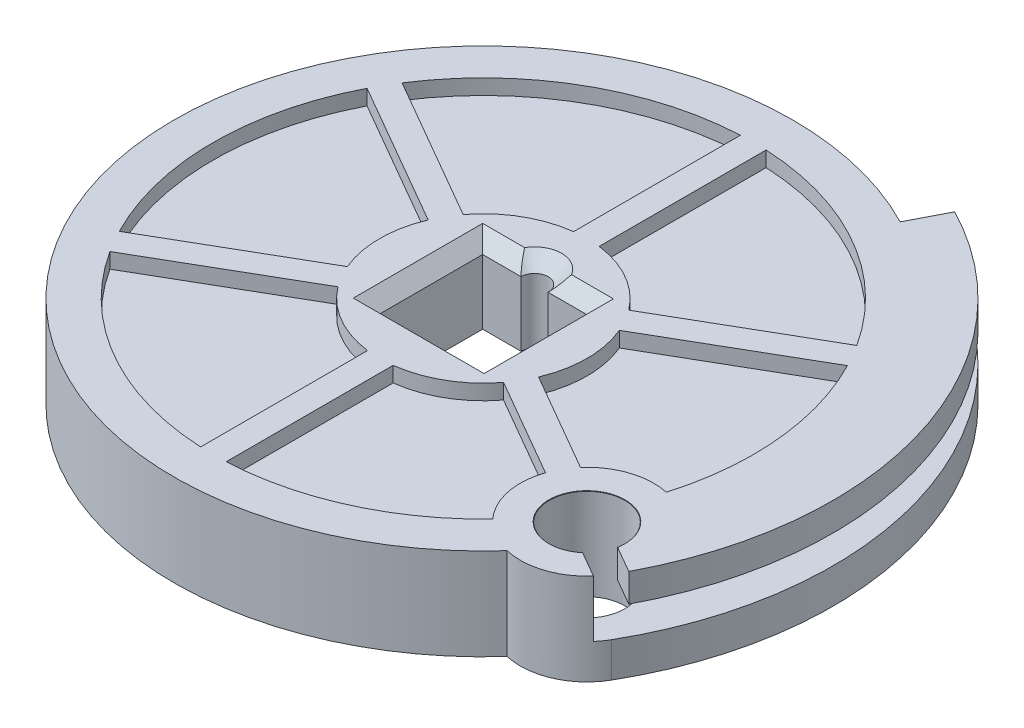
SolidWorks part; units mm, degrees
ref_plane "Plano frontal" through (0, 0, 0) normal (0, 0, 1) x (1, 0, 0)
ref_plane "Plano superior" through (0, 0, 0) normal (0, 1, 0) x (1, 0, 0)
ref_plane "Plano direito" through (0, 0, 0) normal (1, 0, 0) x (0, 0, -1)
sketch "Esboço1" plane through (0, 0, 0) normal (0, 1, 0) x (1, 0, 0)
  line L0 (0, 0) -> (0, 7.7) construction
  line L1 (0, 0) -> (6.6684, 3.85) construction
  line L2 (0, 0) -> (6.6684, -3.85) construction
  line L3 (0, 0) -> (0, -7.7) construction
  line L4 (0, 0) -> (-6.6684, -3.85) construction
  line L5 (0, 0) -> (-6.6684, 3.85) construction
  line L6 (0.95, 0) -> (0.95, 7.6412) construction
  line L7 (-0.95, 0) -> (-0.95, 7.6412) construction
  line L8 (0.475, -0.8227) -> (7.0924, 2.9979) construction
  line L9 (-0.475, 0.8227) -> (6.1424, 4.6433) construction
  line L10 (-0.475, -0.8227) -> (6.1424, -4.6433) construction
  line L11 (0.475, 0.8227) -> (7.0924, -2.9979) construction
  line L12 (-0.95, 0) -> (-0.95, -7.6412) construction
  line L13 (0.95, 0) -> (0.95, -7.6412) construction
  line L14 (-0.475, 0.8227) -> (-7.0924, -2.9979) construction
  line L15 (0.475, -0.8227) -> (-6.1424, -4.6433) construction
  line L16 (0.475, 0.8227) -> (-6.1424, 4.6433) construction
  line L17 (-0.475, -0.8227) -> (-7.0924, 2.9979) construction
  line L18 (-7.0924, 2.9979) -> (-17.8193, 9.191)
  line L19 (-17.8193, 9.191) -> (-20.3503, 10.6523) construction
  line L20 (-0.475, -0.8227) -> (-20.3503, 10.6523) construction
  line L21 (-6.6684, 3.85) -> (-17.3638, 10.025) construction
  line L22 (-17.3638, 10.025) -> (-19.8753, 11.475) construction
  line L23 (0, 0) -> (-19.8753, 11.475) construction
  line L24 (-6.1424, 4.6433) -> (-16.8693, 10.8365)
  line L25 (-16.8693, 10.8365) -> (-19.4003, 12.2977) construction
  line L26 (0.475, 0.8227) -> (-19.4003, 12.2977) construction
  line L27 (-0.95, 7.6412) -> (-0.95, 20.0275)
  line L28 (-0.95, 20.0275) -> (-0.95, 22.95) construction
  line L29 (-0.95, 0) -> (-0.95, 22.95) construction
  line L30 (0, 7.7) -> (0, 20.05) construction
  line L31 (0, 20.05) -> (0, 22.95) construction
  line L32 (0, 0) -> (0, 22.95) construction
  line L33 (0.95, 7.6412) -> (0.95, 20.0275)
  line L34 (0.95, 20.0275) -> (0.95, 22.95) construction
  line L35 (0.95, 0) -> (0.95, 22.95) construction
  line L36 (6.1424, 4.6433) -> (16.8693, 10.8365)
  line L37 (16.8693, 10.8365) -> (19.4003, 12.2977) construction
  line L38 (-0.475, 0.8227) -> (19.4003, 12.2977) construction
  line L39 (6.6684, 3.85) -> (17.3638, 10.025) construction
  line L40 (17.3638, 10.025) -> (19.8753, 11.475) construction
  line L41 (0, 0) -> (19.8753, 11.475) construction
  line L42 (7.0924, 2.9979) -> (17.8193, 9.191)
  line L43 (17.8193, 9.191) -> (20.3503, 10.6523) construction
  line L44 (0.475, -0.8227) -> (20.3503, 10.6523) construction
  line L45 (7.0924, -2.9979) -> (17.8193, -9.191)
  line L46 (17.8193, -9.191) -> (20.3503, -10.6523) construction
  line L47 (0.475, 0.8227) -> (20.3503, -10.6523) construction
  line L48 (6.6684, -3.85) -> (17.3638, -10.025) construction
  line L49 (17.3638, -10.025) -> (19.8753, -11.475) construction
  line L50 (0, 0) -> (19.8753, -11.475) construction
  line L51 (6.1424, -4.6433) -> (16.8693, -10.8365)
  line L52 (16.8693, -10.8365) -> (19.4003, -12.2977) construction
  line L53 (-0.475, -0.8227) -> (19.4003, -12.2977) construction
  line L54 (0.95, -7.6412) -> (0.95, -20.0275)
  line L55 (0.95, -20.0275) -> (0.95, -22.95) construction
  line L56 (0.95, 0) -> (0.95, -22.95) construction
  line L57 (0, -7.7) -> (0, -20.05) construction
  line L58 (0, -20.05) -> (0, -22.95) construction
  line L59 (0, 0) -> (0, -22.95) construction
  line L60 (-0.95, -7.6412) -> (-0.95, -20.0275)
  line L61 (-0.95, -20.0275) -> (-0.95, -22.95) construction
  line L62 (-0.95, 0) -> (-0.95, -22.95) construction
  line L63 (-6.1424, -4.6433) -> (-16.8693, -10.8365)
  line L64 (-16.8693, -10.8365) -> (-19.4003, -12.2977) construction
  line L65 (0.475, -0.8227) -> (-19.4003, -12.2977) construction
  line L66 (-6.6684, -3.85) -> (-17.3638, -10.025) construction
  line L67 (-17.3638, -10.025) -> (-19.8753, -11.475) construction
  line L68 (0, 0) -> (-19.8753, -11.475) construction
  line L69 (-7.0924, -2.9979) -> (-17.8193, -9.191)
  line L70 (-17.8193, -9.191) -> (-20.3503, -10.6523) construction
  line L71 (-0.475, 0.8227) -> (-20.3503, -10.6523) construction
  circle A0 centre (0, 0) radius 22.95
  arc A1 (-17.8193, 9.191) -> (-17.8193, -9.191) centre (0, 0) ccw
  arc A2 (-7.0924, 2.9979) -> (-7.0924, -2.9979) centre (0, 0) ccw
  arc A3 (-16.8693, 10.8365) -> (-17.3638, 10.025) centre (0, 0) ccw construction
  arc A4 (-17.3638, 10.025) -> (-17.8193, 9.191) centre (0, 0) ccw construction
  circle A5 centre (0, 0) radius 20.05 construction
  arc A6 (-0.95, 20.0275) -> (-16.8693, 10.8365) centre (0, 0) ccw
  arc A7 (0, 20.05) -> (-0.95, 20.0275) centre (0, 0) ccw construction
  arc A8 (0.95, 20.0275) -> (0, 20.05) centre (0, 0) ccw construction
  arc A9 (16.8693, 10.8365) -> (0.95, 20.0275) centre (0, 0) ccw
  arc A10 (17.3638, 10.025) -> (16.8693, 10.8365) centre (0, 0) ccw construction
  arc A11 (17.8193, 9.191) -> (17.3638, 10.025) centre (0, 0) ccw construction
  arc A12 (17.8193, -9.191) -> (17.8193, 9.191) centre (0, 0) ccw
  arc A13 (17.3638, -10.025) -> (17.8193, -9.191) centre (0, 0) ccw construction
  arc A14 (16.8693, -10.8365) -> (17.3638, -10.025) centre (0, 0) ccw construction
  arc A15 (0.95, -20.0275) -> (16.8693, -10.8365) centre (0, 0) ccw
  arc A16 (-0.95, -20.0275) -> (0, -20.05) centre (0, 0) ccw construction
  arc A17 (0, -20.05) -> (0.95, -20.0275) centre (0, 0) ccw construction
  arc A18 (-16.8693, -10.8365) -> (-0.95, -20.0275) centre (0, 0) ccw
  arc A19 (-17.8193, -9.191) -> (-17.3638, -10.025) centre (0, 0) ccw construction
  arc A20 (-17.3638, -10.025) -> (-16.8693, -10.8365) centre (0, 0) ccw construction
  arc A21 (-6.1424, 4.6433) -> (-6.6684, 3.85) centre (0, 0) ccw construction
  arc A22 (-6.6684, 3.85) -> (-7.0924, 2.9979) centre (0, 0) ccw construction
  arc A23 (-6.1424, -4.6433) -> (-0.95, -7.6412) centre (0, 0) ccw
  arc A24 (-7.0924, -2.9979) -> (-6.6684, -3.85) centre (0, 0) ccw construction
  arc A25 (-6.6684, -3.85) -> (-6.1424, -4.6433) centre (0, 0) ccw construction
  arc A26 (-0.95, 7.6412) -> (-6.1424, 4.6433) centre (0, 0) ccw
  arc A27 (0, 7.7) -> (-0.95, 7.6412) centre (0, 0) ccw construction
  arc A28 (0.95, 7.6412) -> (0, 7.7) centre (0, 0) ccw construction
  arc A29 (6.1424, 4.6433) -> (0.95, 7.6412) centre (0, 0) ccw
  arc A30 (6.6684, 3.85) -> (6.1424, 4.6433) centre (0, 0) ccw construction
  arc A31 (7.0924, 2.9979) -> (6.6684, 3.85) centre (0, 0) ccw construction
  arc A32 (7.0924, -2.9979) -> (7.0924, 2.9979) centre (0, 0) ccw
  arc A33 (6.1424, -4.6433) -> (6.6684, -3.85) centre (0, 0) ccw construction
  arc A34 (6.6684, -3.85) -> (7.0924, -2.9979) centre (0, 0) ccw construction
  arc A35 (0.95, -7.6412) -> (6.1424, -4.6433) centre (0, 0) ccw
  arc A36 (0, -7.7) -> (0.95, -7.6412) centre (0, 0) ccw construction
  arc A37 (-0.95, -7.6412) -> (0, -7.7) centre (0, 0) ccw construction
  point P13 (0, 0)
  point P73 (20.05, 0)
  dimension "D1" = 45.9
  dimension "D16" = 15.4
  dimension "D2" = 2.9
  dimension "D4" = 0.95
  dimension "D5" = 0.95
  dimension "D6" = 0.95
  dimension "D7" = 0.95
  dimension "D8" = 0.95
  dimension "D9" = 0.95
  dimension "D10" = 0.95
  dimension "D11" = 0.95
  dimension "D12" = 0.95
  dimension "D13" = 0.95
  dimension "D14" = 0.95
  dimension "D15" = 0.95
  dimension "D3" = 6
extrude "Ressalto-extrusão1" add sketch "Esboço1" along normal mid plane 6.8
sketch "Esboço2" plane through (0, 0, 0) normal (0, 1, 0) x (1, 0, 0)
  circle A0 centre (0, 0) radius 22.95 construction
  circle A1 centre (0, 0) radius 22.95
extrude "Ressalto-extrusão2" add sketch "Esboço2" along normal blind 2.2667
sketch "Esboço3" plane through (0, 3.4, 0) normal (0, 1, 0) x (1, 0, 0)
  line L0 (1.0048, 3.8) -> (3.85, 3.8)
  line L1 (-3.85, 3.8) -> (-1.0048, 3.8)
  line L2 (-3.85, 3.8) -> (-3.85, -3.8)
  line L3 (-3.85, -3.8) -> (3.85, -3.8)
  line L4 (3.85, 3.8) -> (3.85, -3.8)
  line L5 (-3.85, 3.8) -> (3.85, -3.8) construction
  line L6 (-3.85, -3.8) -> (3.85, 3.8) construction
  line L7 (-1.0048, 3.8) -> (1.0048, 3.8) construction
  arc A0 (1.0048, 3.8) -> (-1.0048, 3.8) centre (0, 3.8) ccw
  arc A1 (-1.0048, 3.8) -> (1.0048, 3.8) centre (0, 3.8) ccw construction
  point P0 (0, 0)
  point P7 (0, 0)
  dimension "D3" = 1.0048
  dimension "D1" = 7.6
  dimension "D2" = 7.7
extrude "Corte-extrusão1" cut sketch "Esboço3" against normal through all
chamfer "Chanfro1" distance 1 angle 45 12 edges at (-3.85, -3.4, 0) (-2.4274, -3.4, -3.8) (0, -3.4, -4.8048) (2.4274, -3.4, -3.8) (3.85, -3.4, 0) (0, -3.4, 3.8) (0, 3.4, 3.8) (3.85, 3.4, 0) (2.4274, 3.4, -3.8) (0, 3.4, -4.8048) (-2.4274, 3.4, -3.8) (-3.85, 3.4, 0)
sketch "Esboço4" plane through (0, 3.4, 0) normal (0, 1, 0) x (1, 0, 0)
  line L0 (6.6684, -3.85) -> (17.3638, -10.025) construction
  line L1 (22.4734, -12.975) -> (-19.8753, 11.475) construction
  line L2 (9.2074, 17.8109) -> (11.9168, 23.052)
  line L3 (11.9168, 23.052) -> (20.7643, -14.7258) construction
  line L4 (0, 0) -> (9.2074, 17.8109) construction
  arc A0 (19.2339, -5.6621) -> (22.4734, -12.975) centre (18.1865, -10.5) ccw
  arc A1 (22.4734, -12.975) -> (11.9168, 23.052) centre (0, 0) ccw
  arc A2 (11.9168, 23.052) -> (22.4734, -12.975) centre (0, 0) ccw construction
  arc A3 (14.5205, -13.826) -> (17.3638, -10.025) centre (0, 0) ccw construction
  arc A4 (9.2074, 17.8109) -> (-17.3638, 10.025) centre (0, 0) ccw construction
  arc A5 (-17.3638, 10.025) -> (14.5205, -13.826) centre (0, 0) ccw construction
  arc A6 (19.2339, -5.6621) -> (9.2074, 17.8109) centre (0, 0) ccw
  arc A7 (17.3638, -10.025) -> (18.8897, -6.7216) centre (0, 0) ccw construction
  arc A8 (18.8897, -6.7216) -> (19.2339, -5.6621) centre (0, 0) ccw construction
  arc A9 (22.4734, -12.975) -> (19.2339, -5.6621) centre (18.1865, -10.5) ccw construction
  dimension "D1" = 9.9
  dimension "D2" = 48.9
  dimension "D4" = 92.663
extrude "Ressalto-extrusão3" add sketch "Esboço4" against normal up to surface (6.8 mm away) up to face at (0, -3.4, -1.7675)
sketch "Esboço5" plane through (0, 3.4, 0) normal (0, 1, 0) x (1, 0, 0)
  point P0 (18.1865, -10.5)
hole_wizard "Furo de diâmetro Ø5.6 (5.6)1" positions "Esboço5" profile "Esboço6" hole size "Ø5.6" standard "Ansi Metric"
sketch "Esboço6" plane through (18.1865, 3.4, 10.5) normal (1, 0, 0) x (0, 0, 1)
  line L0 (0, 0) -> (0, 11.6824)
  line L1 (0, 11.6824) -> (2.8, 10)
  line L2 (2.8, 10) -> (2.8, 0.025)
  line L3 (2.8, 0.025) -> (2.825, 0)
  line L5 (2.825, 0) -> (0, 0)
  line L6 (-2.8, 0.025) -> (-2.825, 0) construction
  line L10 (0, 11.6824) -> (-2.8, 10) construction
  line L11 (0, -6.35) -> (0, 107.95) construction
  dimension "Hole Dia." = 5.6
  dimension "Hole Depth" = 10
  dimension "Near C'Sink Dia." = 5.65
  dimension "Near C'Sink Angle" = 90
  dimension "Drill Angle" = 118
sketch "Esboço7" plane through (0, 0, 0) normal (0, 1, 0) x (1, 0, 0)
  line L0 (0, 0) -> (0, 20.05) construction
  circle A0 centre (0, 0) radius 20.05 construction
  circle A1 centre (0, 0) radius 25.95 construction
  arc A2 (22.4734, -12.975) -> (11.9168, 23.052) centre (0, 0) ccw construction
  arc A4 (19.8753, -11.475) -> (0, 22.95) centre (0, 0) ccw
  arc A6 (10.5391, 20.387) -> (17.0831, -15.3255) centre (0, 0) ccw construction
  point P8 (0, 0)
  point P10 (0, 0)
  point P14 (19.8251, -11.5615)
  point P15 (19.8753, -11.475)
  point P16 (0, 23)
  point P17 (0, 0)
  point P21 (0, 0)
  point P22 (0, 0)
sketch "Esboço8" plane through (0, 0, 0) normal (1, 0, 0) x (0, 0, -1)
  line L0 (-22.95, -3.4) -> (22.95, -3.4) construction
  line L1 (22.95, 1.3) -> (30.8871, 1.3)
  line L2 (22.95, 1.3) -> (22.95, -0.8)
  line L3 (22.95, -0.8) -> (30.8871, -0.8)
  line L4 (30.8871, 1.3) -> (30.8871, -0.8)
  line L5 (22.95, 3.4) -> (-22.95, 3.4) construction
  point P0 (22.95, 0)
  point P8 (23.4562, 1.0144)
  point P11 (0, 0)
  point P12 (30.8871, -0.8)
  dimension "D1" = 2.6
  dimension "D2" = 2.1
sweep "Varredura de corte1" cut profiles "Esboço8" path "Esboço7"
sketch "Esboço9" plane through (0, 3.4, 0) normal (0, 1, 0) x (1, 0, 0)
  line L0 (18.147, -11.5742) -> (23.0414, -14.3999)
  line L1 (23.0414, -14.3999) -> (24.5391, -13.0707)
  line L2 (24.5391, -13.0707) -> (18.226, -9.4258)
  line L3 (13.5044, -8.8937) -> (6.1424, -4.6433) construction
  line L4 (7.0924, -2.9979) -> (14.4544, -7.2483) construction
  line L5 (18.226, -9.4258) -> (18.147, -11.5742)
  point P8 (18.1865, -10.5)
extrude "Corte-extrusão2" cut sketch "Esboço9" against normal up to surface (4.2 mm away) up to face at (20.0703, -0.8, -2.6508)
